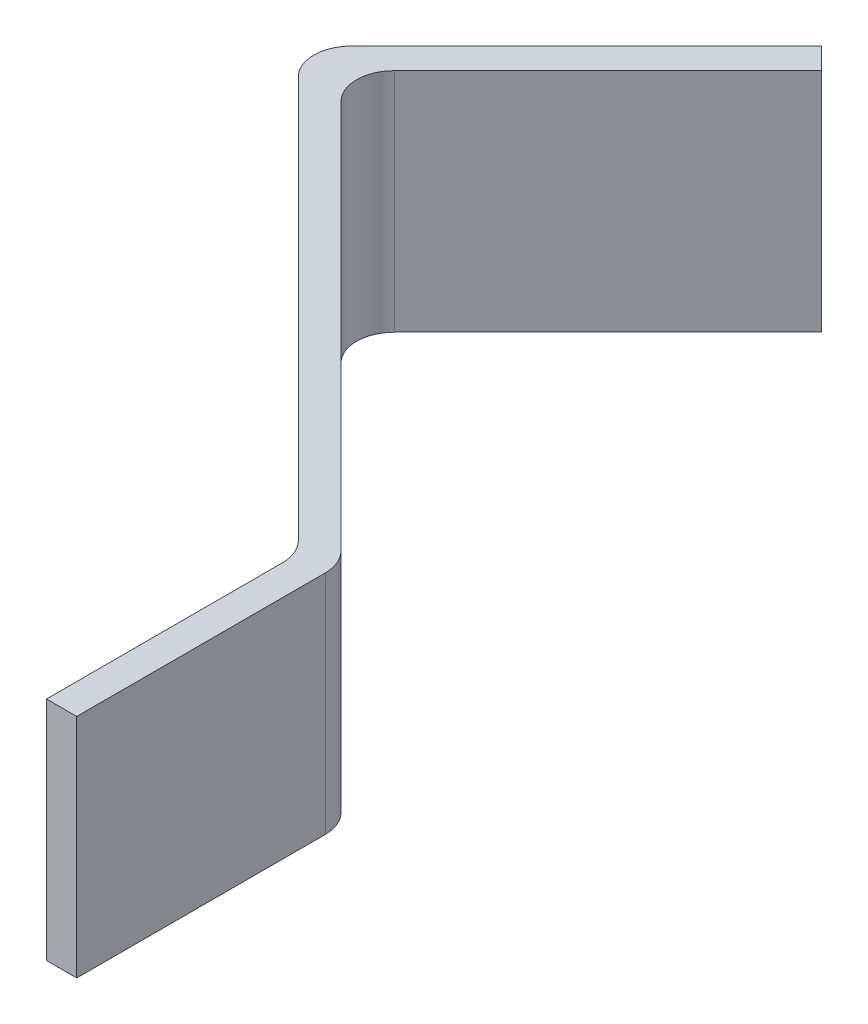
SolidWorks part; units mm, degrees
ref_plane "Front Plane" through (0, 0, 0) normal (0, 0, 1) x (1, 0, 0)
ref_plane "Top Plane" through (0, 0, 0) normal (0, 1, 0) x (1, 0, 0)
ref_plane "Right Plane" through (0, 0, 0) normal (1, 0, 0) x (0, 0, -1)
ref_plane "Plane1" through (0, 7.5, 0) normal (0, 1, 0) x (1, 0, 0)
sketch "Sketch1" plane through (0, 7.5, 0) normal (0, 1, 0) x (1, 0, 0)
  line B0 (-248.7921, 464.6899) -> (-195.5667, 411.4645)
  line B1 (-194.1023, 407.9289) -> (-194.1023, 376.6569)
  line B2 (-194.1023, 376.6569) -> (-190.1023, 376.6569)
  line B3 (-190.1023, 376.6569) -> (-190.1023, 409.5858)
  line B4 (-191.5667, 413.1213) -> (-243.1353, 464.6899)
  line B5 (-243.1353, 471.7609) -> (-214.851, 500.0452)
  line B6 (-214.851, 500.0452) -> (-217.6794, 502.8736)
  line B7 (-217.6794, 502.8736) -> (-248.7921, 471.7609)
  arc B8 (-248.7921, 471.7609) -> (-248.7921, 464.6899) centre (-245.2566, 468.2254) ccw
  arc B9 (-194.1023, 407.9289) -> (-195.5667, 411.4645) centre (-199.1023, 407.9289) ccw
  arc B10 (-190.1023, 409.5858) -> (-191.5667, 413.1213) centre (-195.1023, 409.5858) ccw
  arc B11 (-243.1353, 471.7609) -> (-243.1353, 464.6899) centre (-239.5997, 468.2254) ccw
sketch_block_instance "Block1-1"
sketch_block "Block1"
extrude "Boss-Extrude1" add sketch "Sketch1" against normal blind 30
